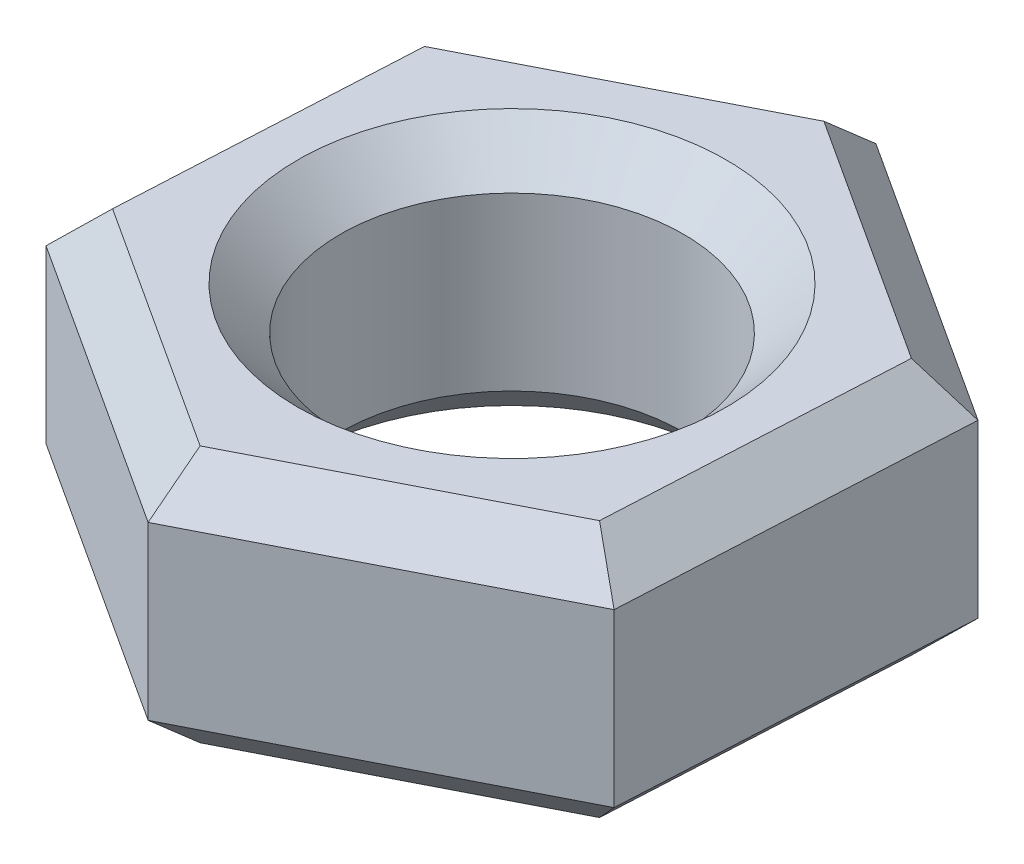
SolidWorks part; units mm, degrees
ref_plane "Front Plane" through (0, 0, 0) normal (0, 0, 1) x (1, 0, 0)
ref_plane "Top Plane" through (0, 0, 0) normal (0, 1, 0) x (1, 0, 0)
ref_plane "Right Plane" through (0, 0, 0) normal (1, 0, 0) x (0, 0, -1)
sketch "Sketch1" plane through (0, 0, 0) normal (0, 1, 0) x (1, 0, 0)
  line L1 (6.7812, -4.3986) -> (7.2, 3.6734)
  line L2 (7.2, 3.6734) -> (0.4187, 8.0721)
  line L3 (0.4187, 8.0721) -> (-6.7812, 4.3986)
  line L4 (-6.7812, 4.3986) -> (-7.2, -3.6734)
  line L5 (-7.2, -3.6734) -> (-0.4187, -8.0721)
  line L6 (-0.4187, -8.0721) -> (6.7812, -4.3986)
  circle A0 centre (0, 0) radius 7 construction
  circle A1 centre (0, 0) radius 4
  dimension "D2" = 8
  dimension "D1" = 14
extrude "Boss-Extrude1" add sketch "Sketch1" along normal blind 6
chamfer "Chamfer1" distance 1 angle 45 14 edges at (0, 6, 4) (-3.8093, 6, 5.8727) (-6.9906, 6, -0.3626) (-3.1813, 6, -6.2353) (3.8093, 6, -5.8727) (6.9906, 6, 0.3626) (3.1813, 6, 6.2353) (0, 0, 4) (6.9906, 0, 0.3626) (3.8093, 0, -5.8727) (-3.1813, 0, -6.2353) (-6.9906, 0, -0.3626) (-3.8093, 0, 5.8727) (3.1813, 0, 6.2353)
